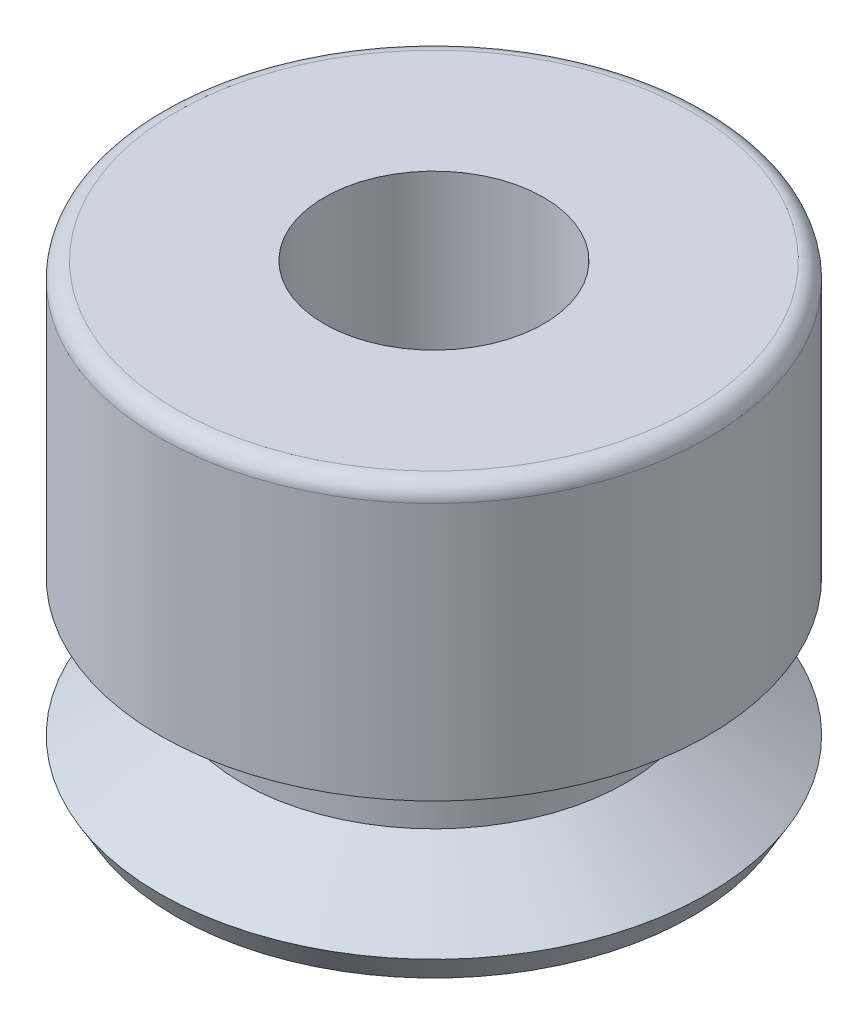
SolidWorks part; units mm, degrees
ref_plane "Front" through (0, 0, 0) normal (0, 0, 1) x (1, 0, 0)
ref_plane "Top" through (0, 0, 0) normal (0, 1, 0) x (1, 0, 0)
ref_plane "Right" through (0, 0, 0) normal (1, 0, 0) x (0, 0, -1)
ref_plane "Plane1" through (0, 0, 0) normal (0, 0, 1) x (1, 0, 0)
sketch "Sketch1" plane through (0, 0, 0) normal (0, 0, 1) x (1, 0, 0)
  line L0 (0, 8) -> (4.7, 8)
  line L1 (5, 7.7) -> (5, 3)
  line L2 (5, 3) -> (3.5, 2)
  line L3 (3.5, 2) -> (3.5, 1.5)
  line L4 (3.5, 1.5) -> (5, 0.5)
  line L5 (5, 0.5) -> (4.7113, 0)
  line L6 (4.7113, 0) -> (0, 0)
  line L7 (0, 0) -> (0, 8)
  line L8 (0, 0) -> (0, 8) construction
  arc A0 (4.7, 8) -> (5, 7.7) centre (4.7, 7.7) cw
revolve "Revolve1" add sketch "Sketch1" angle 360 about L8
ref_plane "Plane2" through (0, 0, 0) normal (0, 0, 1) x (1, 0, 0)
sketch "Sketch2" plane through (0, 0, 0) normal (0, 0, 1) x (1, 0, 0)
  line L0 (0, 8) -> (2, 8)
  line L1 (2, 8) -> (2, 5)
  line L2 (2, 5) -> (3, 5)
  line L3 (3, 5) -> (3, 1)
  line L4 (3, 1) -> (4.7113, 0)
  line L5 (4.7113, 0) -> (0, 0)
  line L6 (0, 0) -> (0, 8)
  line L7 (0, 0) -> (0, 8) construction
revolve "Cut-Revolve1" cut sketch "Sketch2" angle 360 about L7
